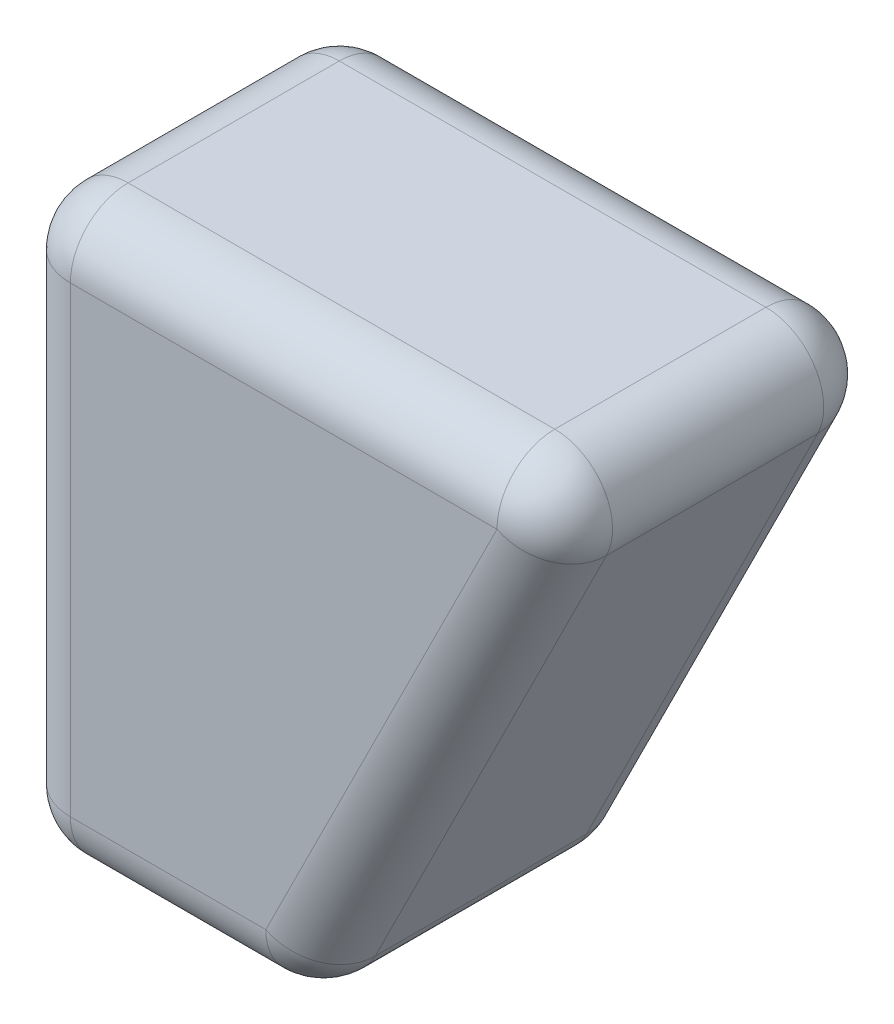
SolidWorks part; units mm, degrees
ref_plane "Plan de face" through (0, 0, 0) normal (0, 0, 1) x (1, 0, 0)
ref_plane "Plan de dessus" through (0, 0, 0) normal (0, 1, 0) x (1, 0, 0)
ref_plane "Plan de droite" through (0, 0, 0) normal (1, 0, 0) x (0, 0, -1)
sketch "Esquisse1" plane through (0, 0, 0) normal (0, 0, 1) x (1, 0, 0)
  line L1 (50, -69.2292) -> (100, 30.7708)
  line L2 (100, 30.7708) -> (0, 30.7708)
  line L3 (100, 30.7708) -> (0, 30.7708) construction
  line L4 (0, 30.7708) -> (0, -69.2292)
  line L5 (0, -69.2292) -> (50, -69.2292)
extrude "Boss.-Extru.1" add sketch "Esquisse1" against normal up to surface (56.5363 mm away) contours L2 L4 L5 L1
fillet "Congé1" radius 10 12 edges at (75, -19.2292, -56.5363) (100, 30.7708, -28.2682) (50, 30.7708, -56.5363) (75, -19.2292, 0) (50, 30.7708, 0) (0, -19.2292, 0) (25, -69.2292, 0) (0, 30.7708, -28.2682) (0, -19.2292, -56.5363) (0, -69.2292, -28.2682) (25, -69.2292, -56.5363) (50, -69.2292, -28.2682)
